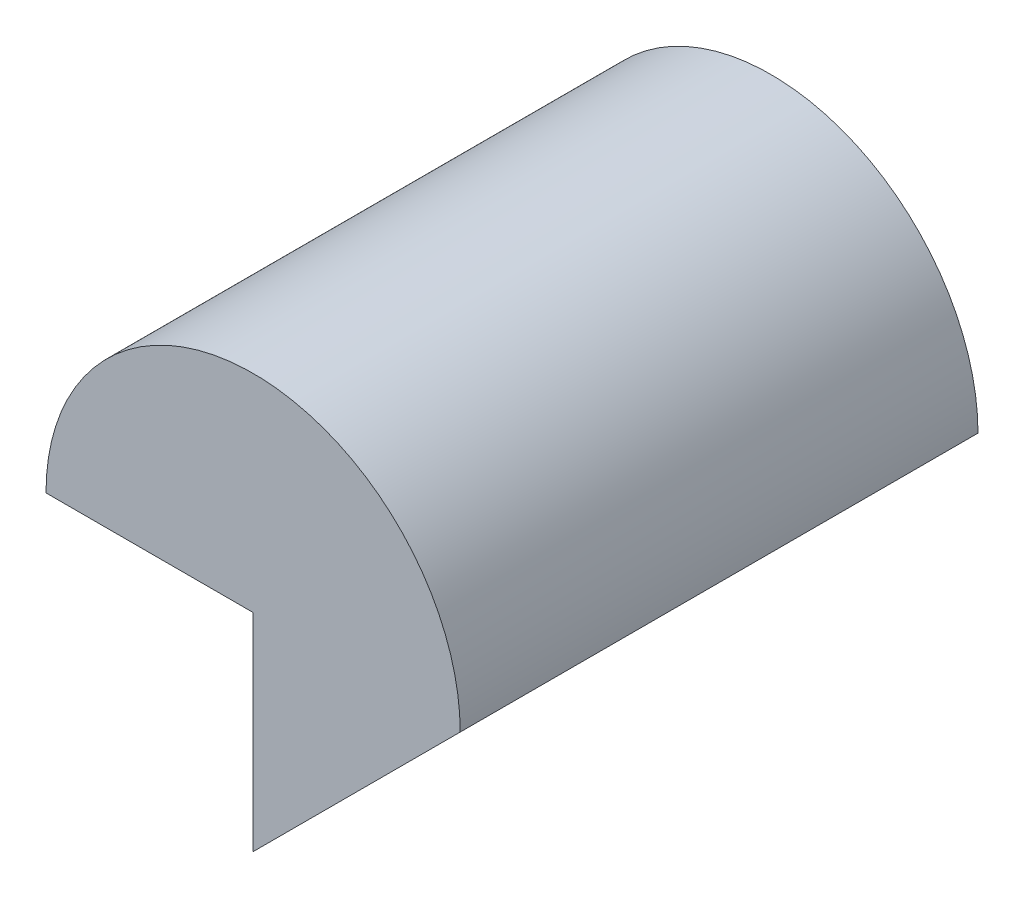
SolidWorks part; units mm, degrees
ref_plane "Front Plane" through (0, 0, 0) normal (0, 0, 1) x (1, 0, 0)
ref_plane "Top Plane" through (0, 0, 0) normal (0, 1, 0) x (1, 0, 0)
ref_plane "Right Plane" through (0, 0, 0) normal (1, 0, 0) x (0, 0, -1)
sketch "Sketch1" plane through (0, 0, 0) normal (0, 0, 1) x (1, 0, 0)
  line L0 (-10, -10) -> (-10, 0)
  line L1 (-10, 0) -> (-20, 0)
  line L2 (-10, -10) -> (0, 0)
  arc A0 (-20, 0) -> (0, 0) centre (-10, 0) cw
  dimension "D1" = 10
  dimension "D2" = 10
  dimension "D3" = 10
extrude "Boss-Extrude1" add sketch "Sketch1" along normal blind 25
